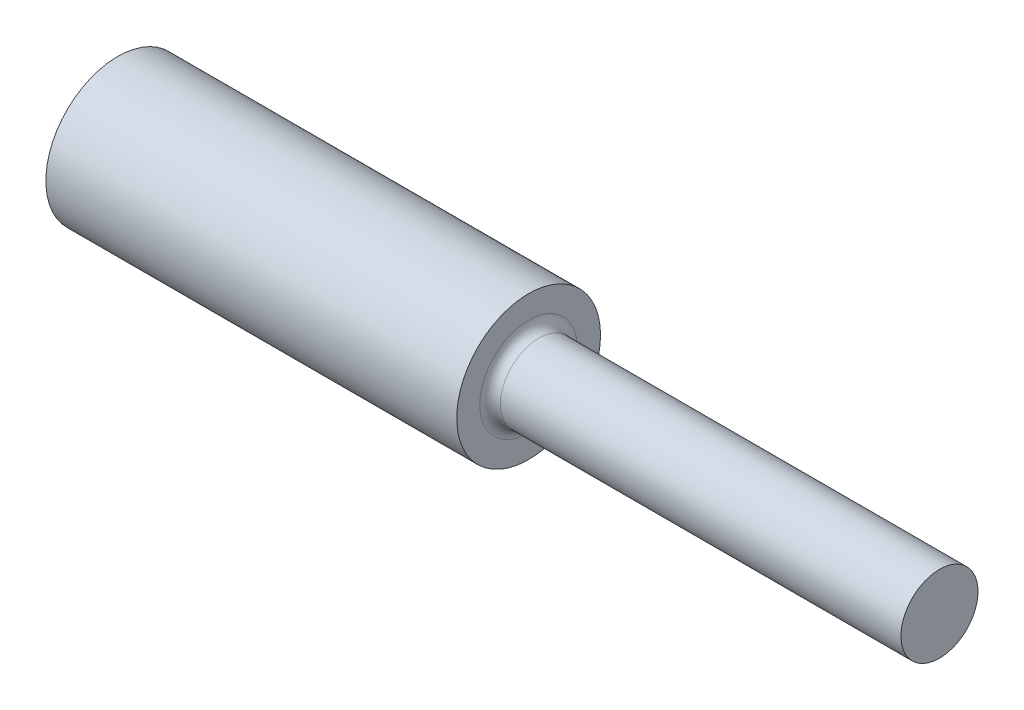
SolidWorks part; units mm, degrees
ref_plane "Front Plane" through (0, 0, 0) normal (0, 0, 1) x (1, 0, 0)
ref_plane "Top Plane" through (0, 0, 0) normal (0, 1, 0) x (1, 0, 0)
ref_plane "Right Plane" through (0, 0, 0) normal (1, 0, 0) x (0, 0, -1)
sketch "Sketch3" plane through (0, 0, 0) normal (0, 0, -1) x (-1, 0, 0)
  line L0 (-60.4108, 0) -> (165.7063, 0) construction
  line L1 (-101.6, 0) -> (-101.6, 9.525)
  line L2 (-101.6, 9.525) -> (0, 9.525)
  line L3 (0, 9.525) -> (0, 17.78)
  line L4 (0, 17.78) -> (101.6, 17.78)
  line L5 (101.6, 17.78) -> (101.6, 0)
  line L6 (101.6, 0) -> (-101.6, 0)
  dimension "D1" = 101.6
  dimension "D2" = 101.6
  dimension "D3" = 35.56
  dimension "D4" = 19.05
revolve "Revolve1" add sketch "Sketch3" angle 360 about L0
fillet "Fillet2" radius 2.54 1 edges at (0, 0, -9.525)
